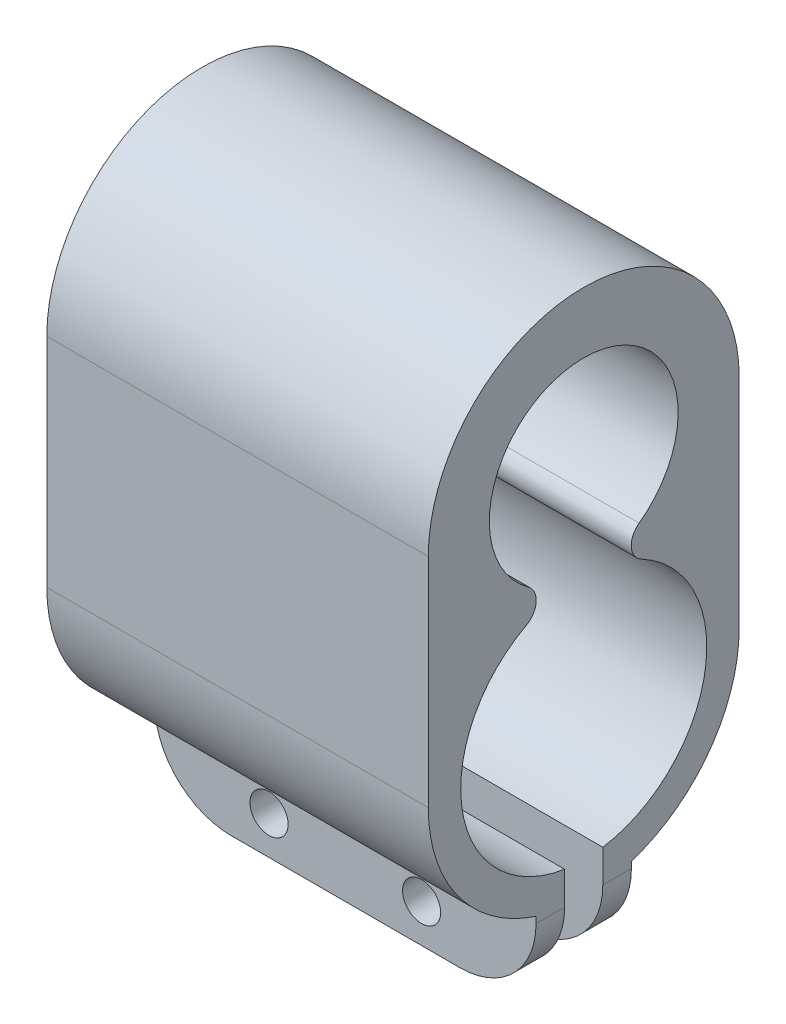
SolidWorks part; units mm, degrees
ref_plane "Front Plane" through (0, 0, 0) normal (0, 0, 1) x (1, 0, 0)
ref_plane "Top Plane" through (0, 0, 0) normal (0, 1, 0) x (1, 0, 0)
ref_plane "Right Plane" through (0, 0, 0) normal (1, 0, 0) x (0, 0, -1)
sketch "Sketch1" plane through (0, 0, 0) normal (1, 0, 0) x (0, 0, -1)
  line L0 (0, 11.4) -> (0, 0) construction
  line L1 (8.15, 11.4) -> (8.15, 0)
  line L2 (-8.15, 11.4) -> (-8.15, 0)
  arc A0 (8.15, 11.4) -> (-8.15, 11.4) centre (0, 11.4) ccw
  arc A1 (-8.15, 0) -> (8.15, 0) centre (0, 0) ccw
  arc A2 (2.9041, 7.3914) -> (-2.9041, 7.3914) centre (0, 11.4) ccw
  arc A3 (-3.0222, 5.6981) -> (3.0222, 5.6981) centre (0, 0) ccw
  arc A4 (-3.0222, 5.6981) -> (-2.9041, 7.3914) centre (-3.4907, 6.5816) ccw
  arc A5 (2.9041, 7.3914) -> (3.0222, 5.6981) centre (3.4907, 6.5816) ccw
  point P3 (0, 5.7)
  dimension "D2" = 9.9
  dimension "D3" = 12.9
  dimension "D4" = 1.7
  dimension "D1" = 11.4
extrude "Boss-Extrude2" add sketch "Sketch1" along normal blind 20
sketch "Sketch2" plane through (20, 0, 0) normal (1, 0, 0) x (0, 0, -1)
  line L0 (0, -6.45) -> (0, -8.15) construction
  line L1 (-1, -2.7425) -> (1, -2.7425)
  line L2 (-1, -2.7425) -> (-1, -11.9852)
  line L3 (-1, -11.9852) -> (1, -11.9852)
  line L4 (1, -2.7425) -> (1, -11.9852)
  arc A0 (-3.0222, 5.6981) -> (3.0222, 5.6981) centre (0, 0) ccw construction
  arc A1 (-8.15, 0) -> (8.15, 0) centre (0, 0) ccw construction
  dimension "D1" = 1
  dimension "D2" = 1
extrude "Cut-Extrude1" cut sketch "Sketch2" against normal blind 20
sketch "Sketch3" plane through (20, 0, 0) normal (1, 0, 0) x (0, 0, -1)
  line L1 (-1, -6.372) -> (-2.5, -6.372)
  line L2 (-1, -6.372) -> (-1, -12.0884)
  line L3 (-1, -12.0884) -> (-2.5, -12.0884)
  line L4 (-2.5, -6.372) -> (-2.5, -12.0884)
  line L5 (1, -6.372) -> (2.5, -6.372)
  line L6 (1, -6.372) -> (1, -12.0884)
  line L7 (1, -12.0884) -> (2.5, -12.0884)
  line L8 (2.5, -6.372) -> (2.5, -12.0884)
  dimension "D1" = 1.5
  dimension "D2" = 1.5
  dimension "D3" = 4
  dimension "D4" = 0
extrude "Boss-Extrude3" add sketch "Sketch3" against normal up to surface (20 mm away) up to face at (0, 2.7447, 0)
sketch "Sketch4" plane through (0, 0, -2.5) normal (0, 0, -1) x (-1, 0, 0)
  line L1 (0, -7.7571) -> (0, -12.0884) construction
  line L2 (-20, -12.0884) -> (-20, -7.7571) construction
  line L3 (0, -12.0884) -> (-20, -12.0884) construction
  line L4 (0, -12.0884) -> (-20, -12.0884) construction
  circle A0 centre (-14, -10.0884) radius 1
  circle A1 centre (-6, -10.0884) radius 1
  dimension "D3" = 2
  dimension "D4" = 2
  dimension "D6" = 2
  dimension "D1" = 6
  dimension "D2" = 6
  dimension "D5" = 2
extrude "Cut-Extrude2" cut sketch "Sketch4" against normal through all
fillet "Fillet1" radius 4 4 edges at (0, -12.0884, 1.75) (20, -12.0884, 1.75) (0, -12.0884, -1.75) (20, -12.0884, -1.75)
